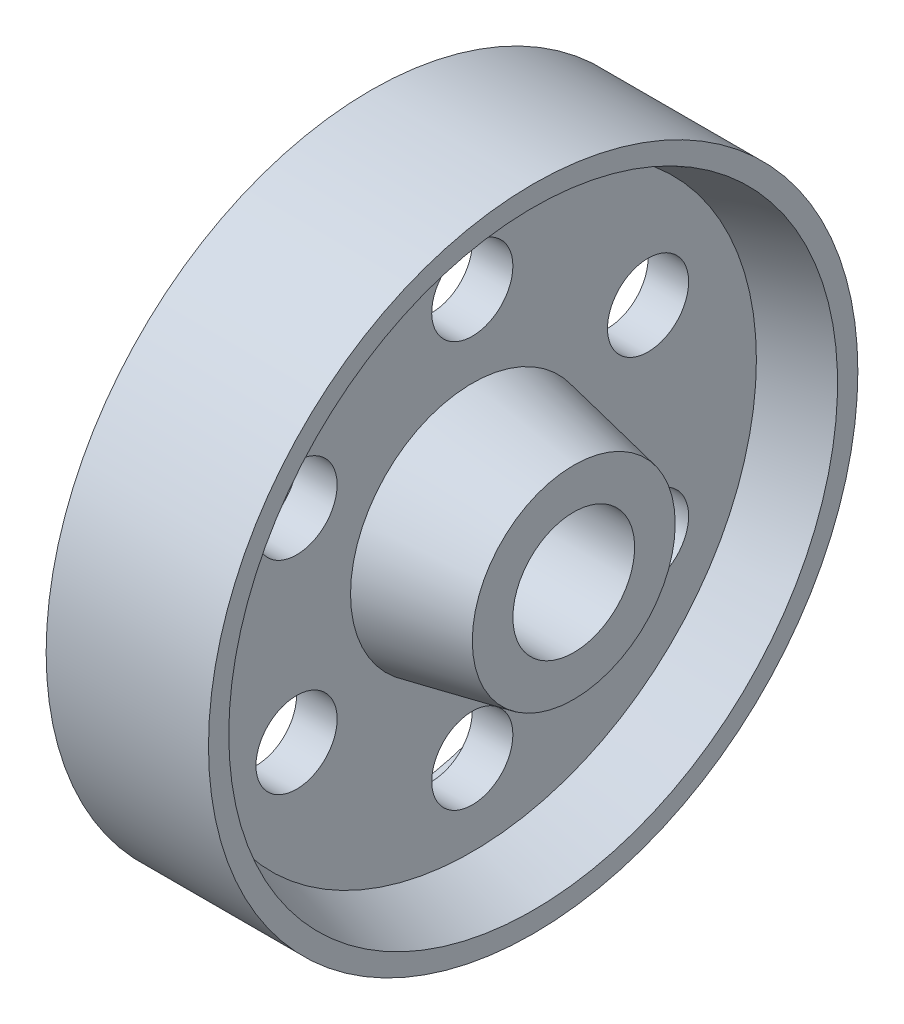
SolidWorks part; units mm, degrees
ref_plane "Front Plane" through (0, 0, 0) normal (0, 0, 1) x (1, 0, 0)
ref_plane "Top Plane" through (0, 0, 0) normal (0, 1, 0) x (1, 0, 0)
ref_plane "Right Plane" through (0, 0, 0) normal (1, 0, 0) x (0, 0, -1)
sketch "Sketch1" plane through (0, 0, 0) normal (0, 0, 1) x (1, 0, 0)
  line L0 (0, 0.375) -> (0.75, 0.375)
  line L1 (0.75, 0.375) -> (0.75, 0.625)
  line L2 (0.75, 0.625) -> (0.125, 0.75)
  line L3 (0.125, 0.75) -> (0.125, 1.75)
  line L4 (0.125, 1.75) -> (0.5, 1.875)
  line L5 (0.5, 1.875) -> (0.5, 2)
  line L6 (0.5, 2) -> (0, 2)
  line L7 (0, 2) -> (0, 0.375)
  line L8 (0, 0) -> (1.046, 0) construction
  dimension "D1" = 0.375
  dimension "D2" = 0.625
  dimension "D3" = 0.75
  dimension "D4" = 0.75
  dimension "D5" = 0.5
  dimension "D6" = 0.125
  dimension "D7" = 1.75
  dimension "D8" = 1.875
  dimension "D9" = 2
revolve "Revolve1" add sketch "Sketch1" angle 360 about L8
mirror "Mirror1" about plane through (0, 2, 0) normal (1, 0, 0) of "Revolve1"
sketch "Sketch2" plane through (0.125, 0, 0) normal (1, 0, 0) x (0, 0, -1)
  line L0 (0, 0) -> (1.0825, 0.625) construction
  line L1 (0, 0) -> (2.5179, 0) construction
  circle A0 centre (1.0825, 0.625) radius 0.25
  circle A1 centre (0, 0) radius 1.25 construction
  dimension "D2" = 0.5
  dimension "D3" = 2.5
  dimension "D1" = 30
extrude "Cut-Extrude2" cut sketch "Sketch2" against normal through all
pattern_circular "CirPattern2" count 6 over 360 about axis through (0, 0, 0) along (1, 0, 0) of "Cut-Extrude2"
